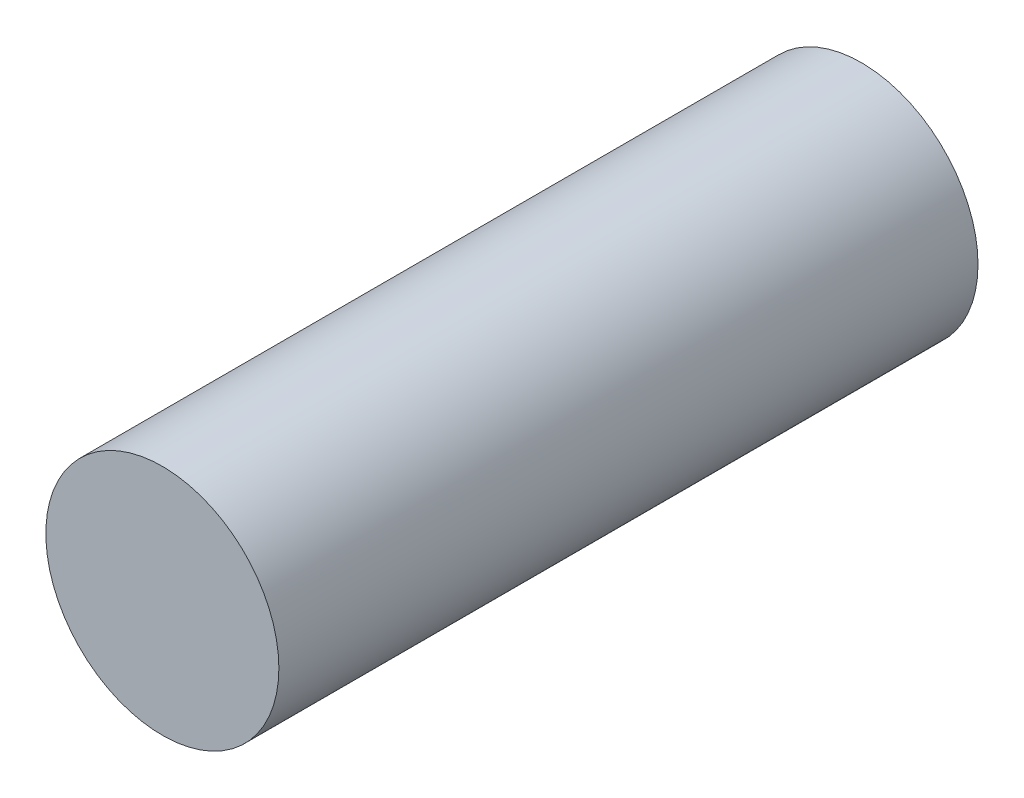
SolidWorks part; units mm, degrees
ref_plane "Front Plane" through (0, 0, 0) normal (0, 0, 1) x (1, 0, 0)
ref_plane "Top Plane" through (0, 0, 0) normal (0, 1, 0) x (1, 0, 0)
ref_plane "Right Plane" through (0, 0, 0) normal (1, 0, 0) x (0, 0, -1)
sketch "Sketch1" plane through (0, 0, 0) normal (0, 0, 1) x (1, 0, 0)
  circle A0 centre (0, 0) radius 3
  dimension "D1" = 6
extrude "Boss-Extrude1" add sketch "Sketch1" along normal blind 18
